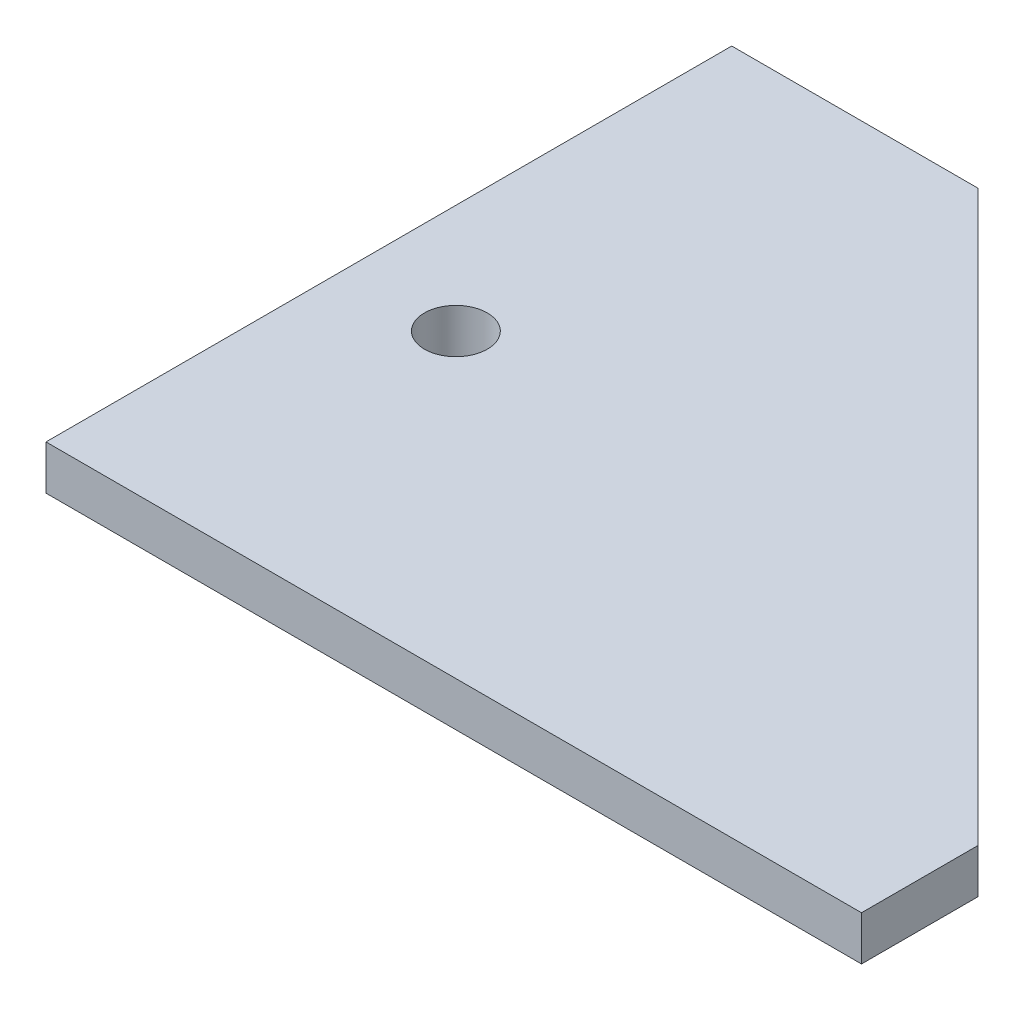
SolidWorks part; units mm, degrees
ref_plane "Front Plane" through (0, 0, 0) normal (0, 0, 1) x (1, 0, 0)
ref_plane "Top Plane" through (0, 0, 0) normal (0, 1, 0) x (1, 0, 0)
ref_plane "Right Plane" through (0, 0, 0) normal (1, 0, 0) x (0, 0, -1)
sketch "Sketch1" plane through (0, 0, 0) normal (0, 1, 0) x (1, 0, 0)
  line L0 (-138.61, 294.305) -> (350, -194.305)
  line L1 (-350, 294.305) -> (-138.61, 294.305)
  line L2 (-350, 294.305) -> (-350, -294.305)
  line L3 (-350, -294.305) -> (350, -294.305)
  line L4 (350, -194.305) -> (350, -294.305)
  line L5 (-350, 294.305) -> (350, -294.305) construction
  point P0 (0, 0)
  dimension "D1" = 588.61
  dimension "D2" = 700
  dimension "D3" = 100
  dimension "D4" = 45
extrude "Boss-Extrude1" add sketch "Sketch1" along normal blind 38.1
sketch "Sketch2" plane through (0, 0, 0) normal (0, -1, 0) x (-1, 0, 0)
  circle A2 centre (256.5002, -35.9805) radius 25 construction
  circle A3 centre (256.5002, -35.9805) radius 25 construction
  circle A4 centre (256.5002, -35.9805) radius 27
  dimension "D1" = 2
extrude "Cut-Extrude1" cut sketch "Sketch2" against normal through all
